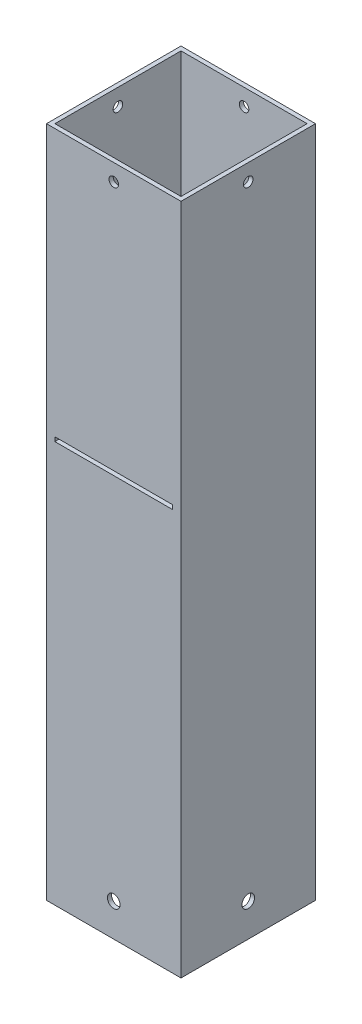
SolidWorks part; units mm, degrees
material "6061 Alloy"
ref_plane "Front Plane" through (0, 0, 0) normal (0, 0, 1) x (1, 0, 0)
ref_plane "Top Plane" through (0, 0, 0) normal (0, 1, 0) x (1, 0, 0)
ref_plane "Right Plane" through (0, 0, 0) normal (1, 0, 0) x (0, 0, -1)
sketch "Sketch1" plane through (0, 0, 0) normal (0, 1, 0) x (1, 0, 0)
  line L1 (-23.8125, 23.8125) -> (23.8125, 23.8125)
  line L2 (-23.8125, 23.8125) -> (-23.8125, -23.8125)
  line L3 (-23.8125, -23.8125) -> (23.8125, -23.8125)
  line L4 (23.8125, 23.8125) -> (23.8125, -23.8125)
  line L5 (-25.4, 25.4) -> (25.4, 25.4)
  line L6 (-25.4, 25.4) -> (-25.4, -25.4)
  line L7 (-25.4, -25.4) -> (25.4, -25.4)
  line L8 (25.4, 25.4) -> (25.4, -25.4)
  point P2 (-25.4, 0)
  point P11 (-23.8125, 0)
  point P12 (0, 23.8125)
  point P13 (0, 25.4)
  dimension "D1" = 47.625
  dimension "1.95" = 47.625
  dimension "2.05" = 50.8
  dimension "D2" = 50.8
extrude "Boss-Extrude1" add sketch "Sketch1" along normal blind 254
ref_plane "Plane1" through (0, 152.4, 0) normal (0, 1, 0) x (1, 0, 0)
sketch "Sketch6" plane through (25.4, 0, 0) normal (1, 0, 0) x (0, 0, -1)
  line L0 (-25.4, 0) -> (25.4, 0) construction
  line L1 (25.4, 254) -> (25.4, 0) construction
  circle A0 centre (0, 12.4124) radius 2.4
  dimension "D1" = 12.4124
  dimension "D2" = 4.8
  dimension "D3" = 25.4
extrude "Cut-Extrude3" cut sketch "Sketch6" against normal through all both and the other way through all
sketch "Sketch7" plane through (0, 0, -25.4) normal (0, 0, -1) x (-1, 0, 0)
  line L0 (-25.4, 0) -> (25.4, 0) construction
  circle A0 centre (0, 12.4124) radius 2.4
  dimension "D1" = 4.8
  dimension "D2" = 12.4124
  dimension "D3" = 25.4
extrude "Cut-Extrude4" cut sketch "Sketch7" against normal through all both
sketch "Sketch8" plane through (25.4, 0, 0) normal (1, 0, 0) x (0, 0, -1)
  line L0 (-25.4, 254) -> (25.4, 254) construction
  line L1 (-25.4, 254) -> (-25.4, 0) construction
  circle A0 centre (0, 247.65) radius 1.8034
  dimension "D1" = 3.6068
  dimension "D2" = 6.35
  dimension "D3" = 25.4
extrude "Cut-Extrude5" cut sketch "Sketch8" against normal through all
sketch "Sketch9" plane through (0, 0, 25.4) normal (0, 0, 1) x (1, 0, 0)
  line L0 (-25.4, 254) -> (-25.4, 0) construction
  line L1 (-25.4, 254) -> (25.4, 254) construction
  circle A0 centre (0, 247.65) radius 1.8034
  dimension "D1" = 3.6068
  dimension "D2" = 25.4
  dimension "D3" = 6.35
extrude "Cut-Extrude6" cut sketch "Sketch9" against normal through all
sketch "Sketch10" plane through (0, 0, 25.4) normal (0, 0, 1) x (1, 0, 0)
  line L1 (-22.225, 153.1937) -> (22.225, 153.1937)
  line L2 (-22.225, 153.1937) -> (-22.225, 151.6062)
  line L3 (-22.225, 151.6062) -> (22.225, 151.6062)
  line L4 (22.225, 153.1937) -> (22.225, 151.6062)
  line L5 (-25.4, 254) -> (-25.4, 0) construction
  line L6 (25.4, 254) -> (25.4, 0) construction
  line L7 (27.94, 152.4) -> (-27.94, 152.4) construction
  dimension "D1" = 0.7937
  dimension "D2" = 1.5875
  dimension "D3" = 3.175
  dimension "D4" = 3.175
extrude "Cut-Extrude7" cut sketch "Sketch10" against normal through all
equation "\"1.95@Sketch1\"=2-(1/8)"
equation "\"D1@Sketch1\"=\"1.95@Sketch1\""
